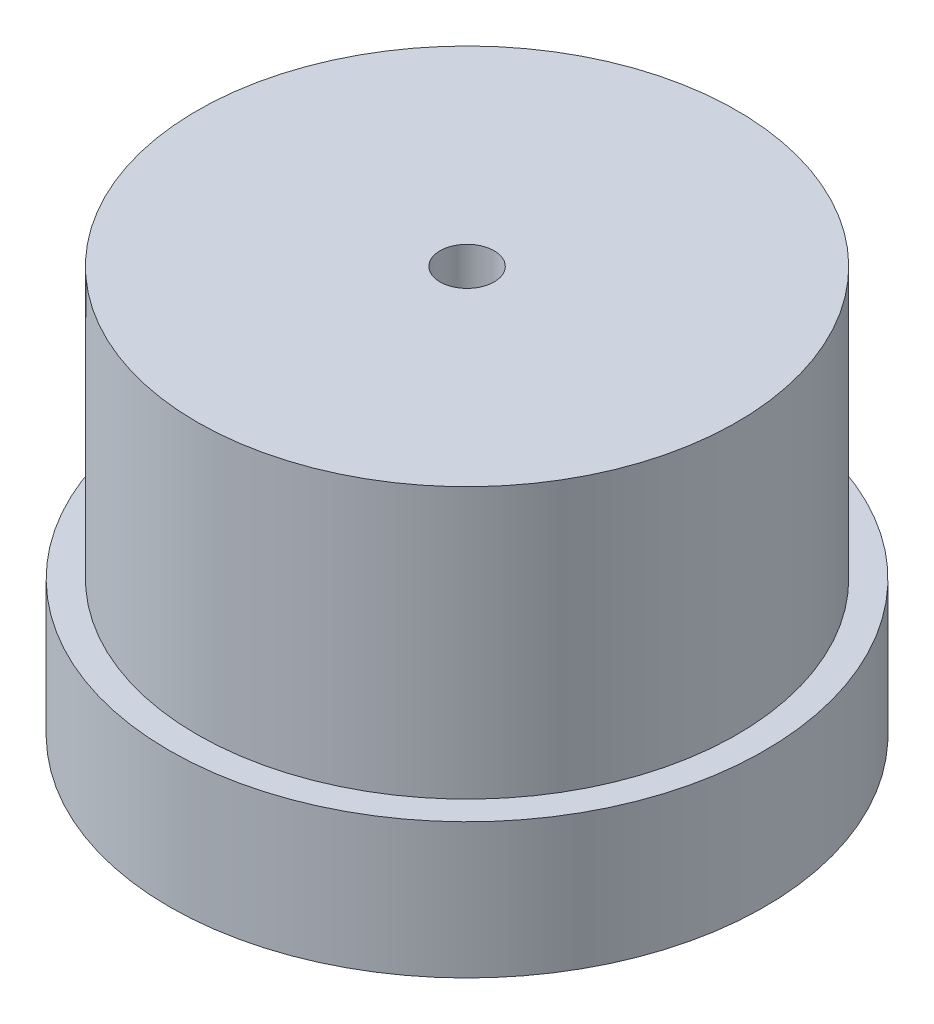
SolidWorks part; units mm, degrees
ref_plane "Front Plane" through (0, 0, 0) normal (0, 0, 1) x (1, 0, 0)
ref_plane "Top Plane" through (0, 0, 0) normal (0, 1, 0) x (1, 0, 0)
ref_plane "Right Plane" through (0, 0, 0) normal (1, 0, 0) x (0, 0, -1)
sketch "Sketch1" plane through (0, 0, 0) normal (0, 1, 0) x (1, 0, 0)
  circle A1 centre (0, 0) radius 22
  dimension "D2" = 44
extrude "Boss-Extrude2" add sketch "Sketch1" along normal blind 10
sketch "Sketch2" plane through (0, 10, 0) normal (0, 1, 0) x (1, 0, 0)
  circle A0 centre (0, 0) radius 19.95
  dimension "D1" = 39.9
extrude "Boss-Extrude3" add sketch "Sketch2" along normal blind 20
sketch "Sketch3" plane through (0, 30, 0) normal (0, 1, 0) x (1, 0, 0)
  circle A0 centre (0, 0) radius 2
extrude "Cut-Extrude1" cut sketch "Sketch3" against normal through all
